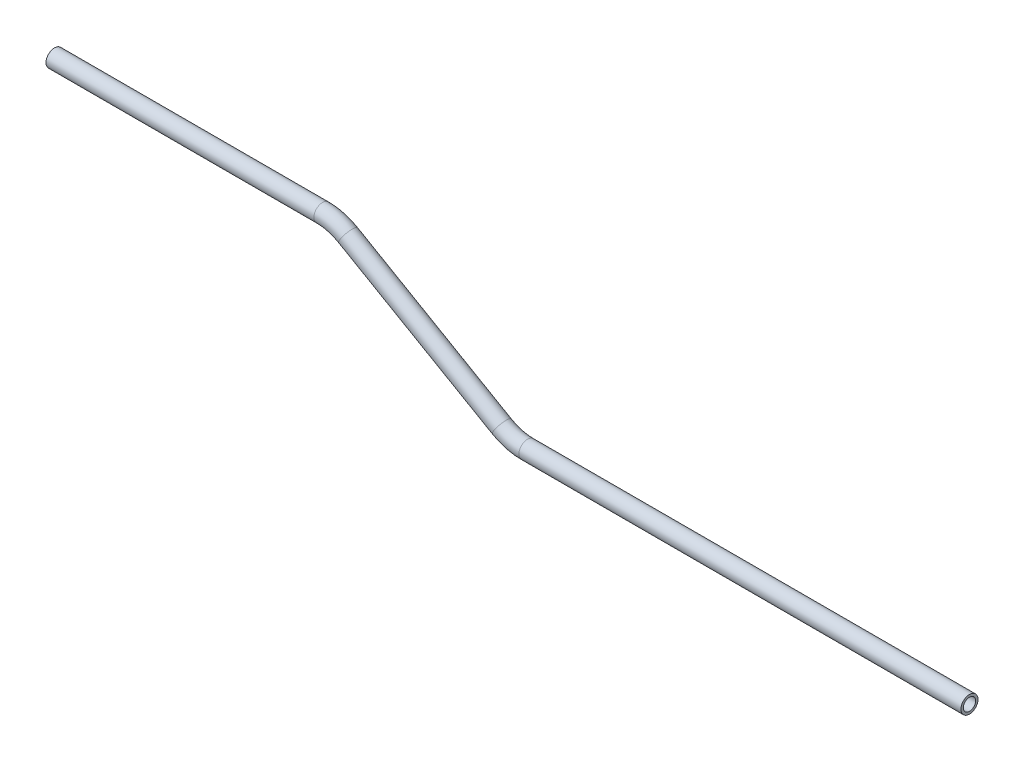
SolidWorks part; units mm, degrees
material "AISI 316 Stainless Steel Sheet (SS)"
ref_plane "Front Plane" through (0, 0, 0) normal (0, 0, 1) x (1, 0, 0)
ref_plane "Top Plane" through (0, 0, 0) normal (0, 1, 0) x (1, 0, 0)
ref_plane "Right Plane" through (0, 0, 0) normal (1, 0, 0) x (0, 0, -1)
sketch "Sketch1" plane through (0, 0, 0) normal (0, 0, 1) x (1, 0, 0)
  line L0 (-56.1298, 3.0743) -> (43.4659, 3.0743)
  line L1 (52.9909, 0.5221) -> (110.1409, -32.4735)
  line L2 (119.6659, -35.0257) -> (283.9794, -35.0257)
  line L11 (119.6659, -35.0257) -> (283.9794, -35.0257) construction
  line L13 (119.6659, -35.0257) -> (44.0246, -35.0257) construction
  line L14 (52.9909, 0.5221) -> (110.1409, -32.4735) construction
  line L15 (110.1409, -32.4735) -> (85.5287, -18.2637) construction
  line L16 (110.1409, -32.4735) -> (52.9909, 0.5221) construction
  line L17 (52.9909, 0.5221) -> (32.226, 12.5107) construction
  line L18 (-56.1298, 3.0743) -> (43.4659, 3.0743) construction
  line L19 (43.4659, 3.0743) -> (68.8451, 3.0743) construction
  arc A0 (43.4659, 3.0743) -> (52.9909, 0.5221) centre (43.4659, -15.9757) cw
  arc A1 (110.1409, -32.4735) -> (119.6659, -35.0257) centre (119.6659, -15.9757) ccw
  point P10 (48.5703, 3.0743)
  point P23 (114.5614, -35.0257)
  dimension "D1" = 19.05
  dimension "D2" = 19.05
  dimension "D3" = 169.418
  dimension "D4" = 38.1
  dimension "D5" = 30
  dimension "D6" = 30
  dimension "D7" = 76.2
  dimension "D12" = 104.7001
ref_plane "Plane1" through (-56.1298, 3.0743, 0) normal (1, 0, 0) x (0, 0, -1)
sketch "Sketch2" plane through (-56.1298, 3.0743, 0) normal (1, 0, 0) x (0, 0, -1)
  circle A0 centre (0, 0) radius 3.175
  circle A1 centre (0, 0) radius 2.286
  dimension "D1" = 4.572
  dimension "D2" = 6.35
sweep "Sweep1" add profiles "Sketch2" path "Sketch1"
